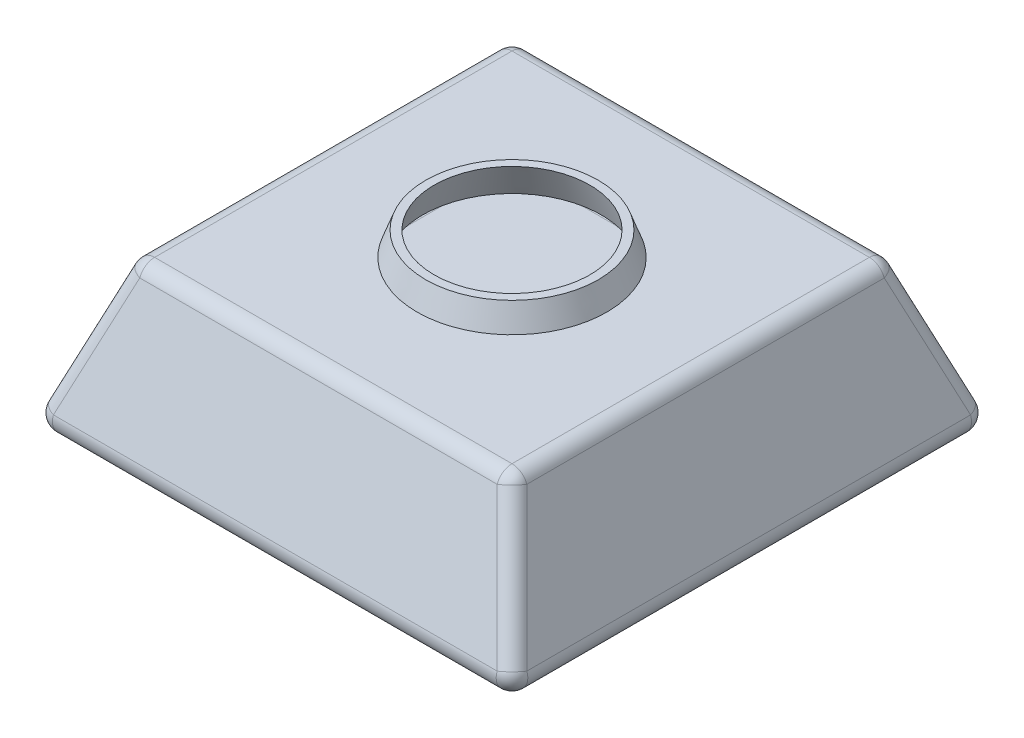
SolidWorks part; units mm, degrees
ref_plane "Front Plane" through (0, 0, 0) normal (0, 0, 1) x (1, 0, 0)
ref_plane "Top Plane" through (0, 0, 0) normal (0, 1, 0) x (1, 0, 0)
ref_plane "Right Plane" through (0, 0, 0) normal (1, 0, 0) x (0, 0, -1)
sketch "Sketch1" plane through (0, 0, 0) normal (0, 1, 0) x (1, 0, 0)
  line L1 (0, 0) -> (480, 0)
  line L2 (0, 0) -> (0, -480)
  line L3 (0, -480) -> (480, -480)
  line L4 (480, 0) -> (480, -480)
  dimension "D1" = 480
  dimension "D2" = 480
extrude "Boss-Extrude1" add sketch "Sketch1" against normal blind 190 draft 20 contours L1 L4 L3 L2 draft outward yes
fillet "Fillet1" radius 20 12 edges at (-34.5772, -95, -34.5772) (514.5772, -95, -34.5772) (549.1543, -190, 240) (240, -190, -69.1543) (-69.1543, -190, 240) (514.5772, -95, 514.5772) (240, -190, 549.1543) (-34.5772, -95, 514.5772) (240, 0, 0) (480, 0, 240) (240, 0, 480) (0, 0, 240)
sketch "Sketch2" plane through (0, 0, 0) normal (0, 1, 0) x (1, 0, 0)
  line L0 (14.0042, -14.0042) -> (465.9958, -465.9958) construction
  circle A0 centre (240, -240) radius 120
  dimension "D1" = 240
extrude "Boss-Extrude2" add sketch "Sketch2" along normal blind 30 draft 20
shell "Shell1" thickness 10
scale "Scale1" scale about origin uniform scaling yes scale factor 0.5
